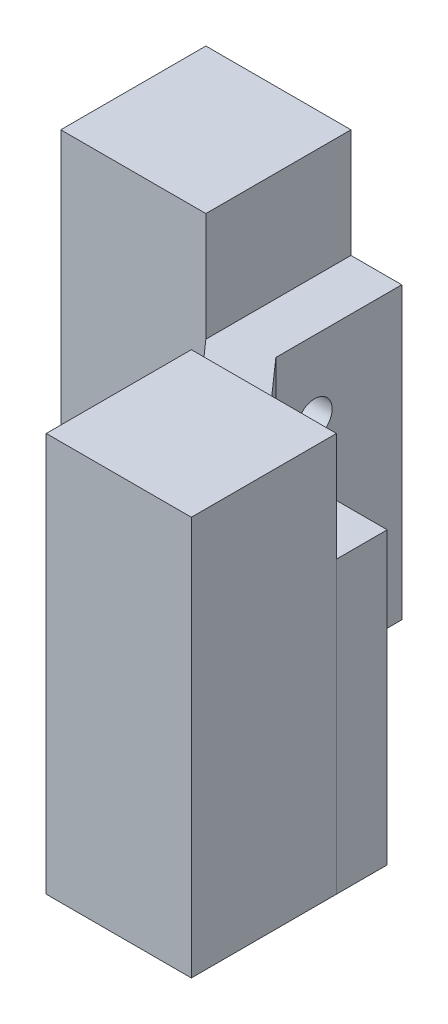
SolidWorks part; units mm, degrees
ref_plane "Front Plane" through (0, 0, 0) normal (0, 0, 1) x (1, 0, 0)
ref_plane "Top Plane" through (0, 0, 0) normal (0, 1, 0) x (1, 0, 0)
ref_plane "Right Plane" through (0, 0, 0) normal (1, 0, 0) x (0, 0, -1)
sketch "Sketch1" plane through (0, 0, 0) normal (0, 1, 0) x (1, 0, 0)
  line L1 (0, 0) -> (-20, 0)
  line L2 (0, 0) -> (0, 20)
  line L3 (0, 20) -> (-20, 20)
  line L4 (-20, 0) -> (-20, 20)
  line L5 (-10, 20) -> (-10, 0) construction
  line L6 (0, 10) -> (-20, 10) construction
  line L7 (15.25, -17.25) -> (35.25, -17.25)
  line L8 (15.25, -17.25) -> (15.25, -37.25)
  line L9 (15.25, -37.25) -> (35.25, -37.25)
  line L10 (35.25, -17.25) -> (35.25, -37.25)
  line L11 (25.25, -37.25) -> (25.25, -17.25) construction
  line L12 (15.25, -27.25) -> (35.25, -27.25) construction
  point P156 (25.25, -27.25)
  point P196 (-10, 10)
  dimension "D1" = 20
  dimension "D2" = 35.25
  dimension "D3" = 37.25
extrude "Boss-Extrude1" add sketch "Sketch1" along normal blind 55
sketch "Sketch2" plane through (0, 0, 0) normal (0, 1, 0) x (1, 0, 0)
  line L0 (-20, 20) -> (0, 20) construction
  line L1 (0, 20) -> (0, 0)
  line L2 (0, 0) -> (15.25, -17.25)
  line L3 (15.25, -17.25) -> (35.25, -17.25)
  line L4 (35.25, -17.25) -> (35.25, -37.25) construction
extrude "Extrude-Thin1" add sketch "Sketch2" along normal blind 40 separate body thin thin type one direction reverse wall 7
hole_wizard "M4 Clearance Hole1" positions "Sketch3" profile "Sketch4" hole size "M4" standard "ANSI Metric" end condition through all
sketch "Sketch3" plane through (0, 0, 10.25) normal (0, 0, -1) x (-1, 0, 0)
  line L0 (-25.25, 30) -> (-25.25, 10) construction
  line L1 (-25.25, 10) -> (-25.25, 0) construction
  line L5 (-25.25, 30) -> (-25.25, 40) construction
  line L8 (-18.4048, 40) -> (-35.25, 40) construction
  line L11 (-35.25, 40) -> (-35.25, 0) construction
  line L12 (-18.4048, 0) -> (-35.25, 0) construction
  point P0 (-25.25, 30)
  point P2 (-25.25, 10)
  point P21 (-31.0528, 63.3898)
  point P24 (-25.8885, 0)
  point P31 (-25.25, 0)
  dimension "D1" = 20
  dimension "D2" = 10
sketch "Sketch4" plane through (25.25, 30, 10.25) normal (1, 0, 0) x (0, 1, 0)
  line L0 (0, 0) -> (0, 27)
  line L1 (0, 27) -> (2.4, 27)
  line L2 (2.4, 27) -> (2.4, 0)
  line L5 (2.4, 0) -> (0, 0)
  line L11 (0, -6.35) -> (0, 107.95) construction
  dimension "Thru Hole Dia." = 4.8
  dimension "Thru Hole Depth" = 27
ref_plane "Plane1" through (8.625, 0, 8.625) normal (-0.7071, 0, -0.7071) x (-0.7071, 0, 0.7071)
mirror "Mirror1" about plane through (8.625, 0, 8.625) normal (-0.7071, 0, -0.7071) of "M4 Clearance Hole1"
